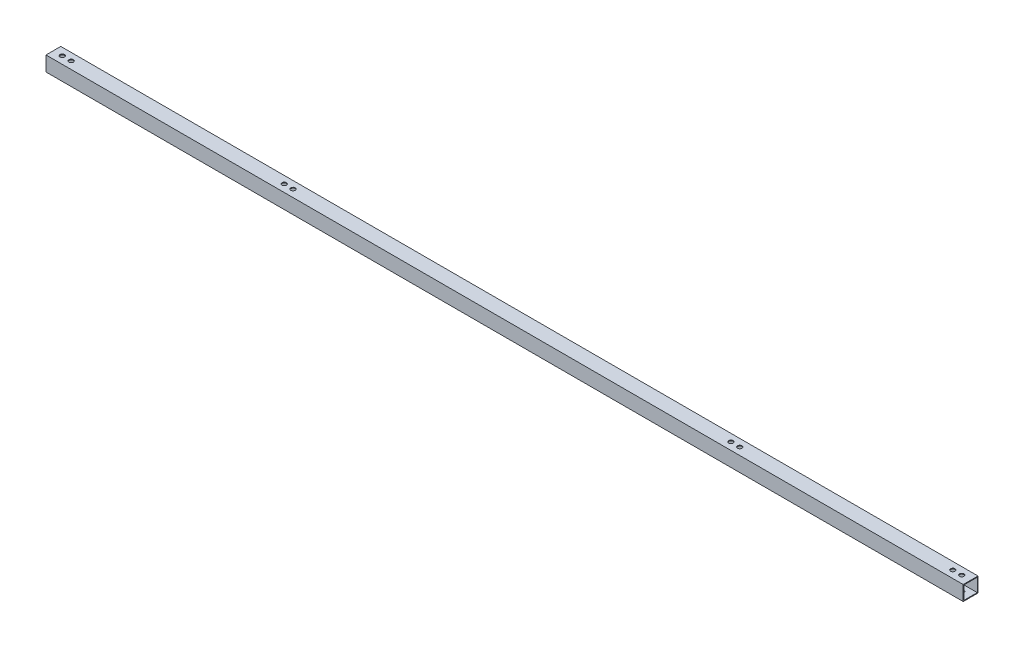
SolidWorks part; units mm, degrees
ref_plane "Front Plane" through (0, 0, 0) normal (0, 0, 1) x (1, 0, 0)
ref_plane "Top Plane" through (0, 0, 0) normal (0, 1, 0) x (1, 0, 0)
ref_plane "Right Plane" through (0, 0, 0) normal (1, 0, 0) x (0, 0, -1)
sketch "Sketch1" plane through (0, 0, 0) normal (1, 0, 0) x (0, 0, -1)
  line L0 (-9, 9) -> (9, 9)
  line L1 (-10, -10) -> (10, -10)
  line L2 (-10, -10) -> (-10, 10)
  line L3 (-10, 10) -> (10, 10)
  line L4 (10, -10) -> (10, 10)
  line L5 (-10, -10) -> (10, 10) construction
  line L6 (-10, 10) -> (10, -10) construction
  line L7 (9, -9) -> (9, 9)
  line L8 (-9, -9) -> (9, -9)
  line L9 (-9, -9) -> (-9, 9)
  point P0 (0, 0)
  dimension "D1" = 20
  dimension "D2" = 20
  dimension "D3" = 1
extrude "Boss-Extrude1" add sketch "Sketch1" along normal blind 1240
sketch "Sketch2" plane through (0, 10, 0) normal (0, 1, 0) x (1, 0, 0)
  line L0 (0, 0) -> (12, 0) construction
  line L1 (620, 10) -> (620, -10) construction
  line L2 (1240, 10) -> (0, 10) construction
  line L3 (1240, -10) -> (0, -10) construction
  circle A0 centre (12, 0) radius 3
  circle A1 centre (24, 0) radius 3
  circle A2 centre (1216, 0) radius 3
  circle A3 centre (1228, 0) radius 3
  circle A4 centre (324, 0) radius 3
  circle A5 centre (312, 0) radius 3
  circle A6 centre (916, 0) radius 3
  circle A7 centre (928, 0) radius 3
extrude "Cut-Extrude1" cut sketch "Sketch2" against normal blind 1240
